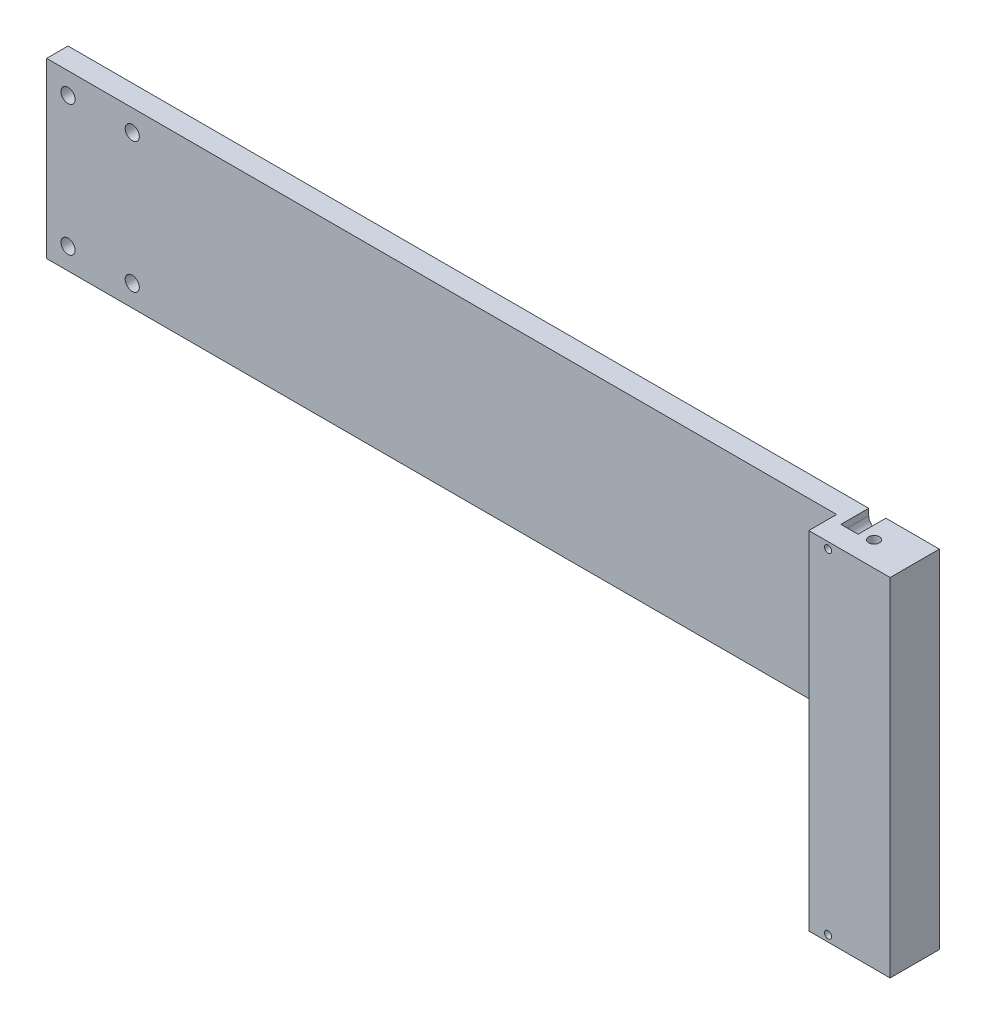
SolidWorks part; units mm, degrees
material "6061 Alloy"
ref_plane "Front Plane" through (0, 0, 0) normal (0, 0, 1) x (1, 0, 0)
ref_plane "Top Plane" through (0, 0, 0) normal (0, 1, 0) x (1, 0, 0)
ref_plane "Right Plane" through (0, 0, 0) normal (1, 0, 0) x (0, 0, -1)
sketch "Sketch1" plane through (0, 0, 0) normal (0, 0, 1) x (1, 0, 0)
  line L1 (0, 0) -> (369, 0)
  line L2 (0, 0) -> (0, 81)
  line L3 (0, 81) -> (369, 81)
  line L4 (369, 0) -> (369, 81)
  dimension "D1" = 81
  dimension "D2" = 369
extrude "Boss-Extrude1" add sketch "Sketch1" along normal blind 10
sketch "Sketch2" plane through (369, 0, 0) normal (1, 0, 0) x (0, 0, -1)
  line L1 (-23, 81) -> (0, 81)
  line L2 (-23, 81) -> (-23, -81)
  line L3 (-23, -81) -> (0, -81)
  line L4 (0, 81) -> (0, -81)
  dimension "D1" = 162
  dimension "D2" = 23
extrude "Boss-Extrude2" add sketch "Sketch2" along normal blind 38
sketch "Sketch3" plane through (0, 0, 0) normal (0, 0, -1) x (-1, 0, 0)
  line L0 (-407, 81) -> (0, 81) construction
  line L1 (0, 81) -> (0, 0) construction
  line L2 (0, 0) -> (-369, 0) construction
  circle A0 centre (-10, 71) radius 3.3
  circle A1 centre (-10, 10) radius 3.3
  circle A2 centre (-40, 10) radius 3.3
  circle A3 centre (-40, 71) radius 3.3
  dimension "D1" = 10
  dimension "D2" = 10
  dimension "D3" = 10
  dimension "D4" = 30
  dimension "D5" = 6.6
  dimension "D6" = 6.6
  dimension "D7" = 6.6
  dimension "D8" = 6.6
extrude "Cut-Extrude1" cut sketch "Sketch3" against normal blind 13
sketch "Sketch4" plane through (0, 81, 0) normal (0, 1, 0) x (1, 0, 0)
  line L0 (407, 0) -> (0, 0) construction
  line L1 (407, 0) -> (407, -23) construction
  circle A0 centre (388, -11.5) radius 2.5
  dimension "D1" = 5
  dimension "D2" = 11.5
  dimension "D3" = 19
extrude "Cut-Extrude2" cut sketch "Sketch4" against normal through all
sketch "Sketch5" plane through (0, 0, 0) normal (0, 0, -1) x (-1, 0, 0)
  line L1 (-407, -81) -> (-407, 81) construction
  line L2 (-407, -81) -> (-369, -81) construction
  line L3 (-407, 81) -> (0, 81) construction
  circle A0 centre (-378, -78) radius 1.65
  circle A1 centre (-378, 78) radius 1.65
  dimension "D1" = 3.3
  dimension "D2" = 29
  dimension "D3" = 3
  dimension "D4" = 3.3
  dimension "D5" = 3
  dimension "D6" = 29
extrude "Cut-Extrude3" cut sketch "Sketch5" against normal through all
sketch "Sketch6" plane through (0, 0, 0) normal (0, 0, -1) x (-1, 0, 0)
  line L0 (-382, -78) -> (-382, -81)
  line L1 (-407, -81) -> (-369, -81) construction
  line L2 (-382, -81) -> (-374, -81)
  line L3 (-374, -81) -> (-374, -78)
  line L4 (-374, 78) -> (-374, 81)
  line L7 (-374, 81) -> (-382, 81)
  line L8 (-407, 81) -> (0, 81) construction
  line L9 (-382, 81) -> (-382, 78)
  arc A0 (-374, -78) -> (-382, -78) centre (-378, -78) ccw
  arc A1 (-382, 78) -> (-374, 78) centre (-378, 78) ccw
  dimension "D1" = 8
  dimension "D2" = 8
  dimension "D3" = 8
  dimension "D4" = 3
extrude "Cut-Extrude4" cut sketch "Sketch6" against normal blind 13
